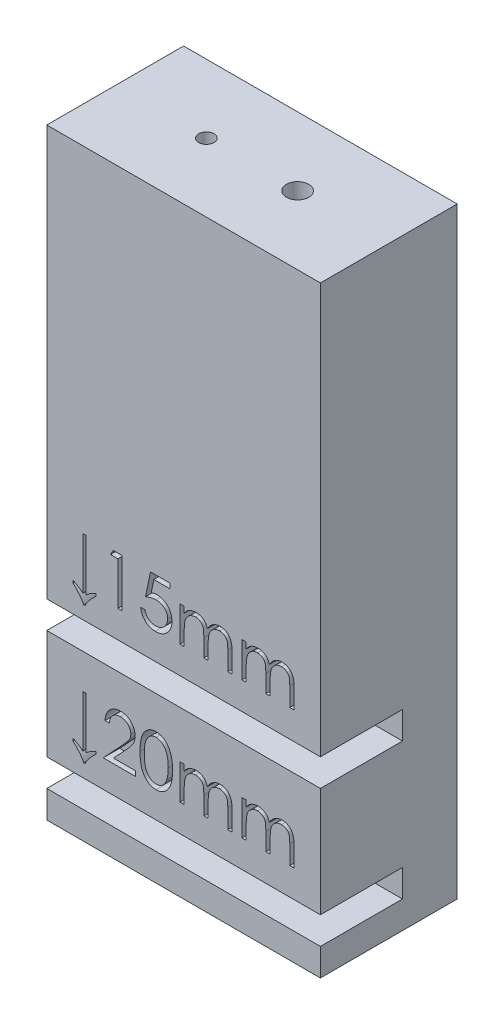
SolidWorks part; units mm, degrees
ref_plane "Front" through (0, 0, 0) normal (0, 0, 1) x (1, 0, 0)
ref_plane "Top" through (0, 0, 0) normal (0, 1, 0) x (1, 0, 0)
ref_plane "Right" through (0, 0, 0) normal (1, 0, 0) x (0, 0, -1)
sketch "Sketch1" plane through (0, 0, 0) normal (0, 1, 0) x (1, 0, 0)
  line L1 (5, 2.5) -> (-5, 2.5)
  line L2 (5, 2.5) -> (5, -2.5)
  line L3 (5, -2.5) -> (-5, -2.5)
  line L4 (-5, 2.5) -> (-5, -2.5)
  line L5 (5, 2.5) -> (-5, -2.5) construction
  line L6 (5, -2.5) -> (-5, 2.5) construction
  point P0 (0, 0)
  dimension "D1" = 10
  dimension "D2" = 5
extrude "Boss-Extrude1" add sketch "Sketch1" along normal blind 22
sketch "Sketch2" plane through (0, 0, 0) normal (0, 1, 0) x (1, 0, 0)
  line L0 (-5, 0) -> (-1.6667, 0) construction
  line L2 (-5, 2.5) -> (-5, -2.5) construction
  line L3 (-1.6667, 0) -> (1.6667, 0) construction
  line L4 (1.6667, 0) -> (5, 0) construction
  line L5 (5, -2.5) -> (5, 2.5) construction
  circle A0 centre (1.6667, 0) radius 0.41
  circle A1 centre (-1.6667, 0) radius 0.28
  dimension "D1" = 0.82
  dimension "D2" = 0.56
extrude "Cut-Extrude2" cut sketch "Sketch2" against normal through all and the other way through all
sketch "Sketch3" plane through (0, 0, 2.5) normal (0, 0, 1) x (1, 0, 0)
  line L4 (-5, 22) -> (-5, 0) construction
  line L5 (5, 7) -> (-5, 7)
  line L6 (0, 22) -> (0, 2) construction
  line L7 (-5, 22) -> (5, 22) construction
  line L8 (-5, 2) -> (5, 2)
  line L9 (-5, 2) -> (-5, 1)
  line L10 (-5, 1) -> (5, 1)
  line L11 (5, 2) -> (5, 1)
  line L12 (-5, 2) -> (5, 1) construction
  line L13 (-5, 1) -> (5, 2) construction
  line L14 (5, 7) -> (5, 6)
  line L15 (-5, 22) -> (-5, 0) construction
  line L16 (5, 6) -> (-5, 6)
  line L17 (-5, 7) -> (-5, 6)
  line L18 (5, 7) -> (-5, 6) construction
  line L19 (5, 6) -> (-5, 7) construction
  line L20 (0, 1) -> (0, 0) construction
  point P0 (0, 6.5)
  point P10 (0, 2)
  point P13 (0, 1.5)
  dimension "D1" = 1
  dimension "D2" = 15
  dimension "D4" = 20
  dimension "D5" = 1
extrude "Cut-Extrude3" cut sketch "Sketch3" against normal offset from surface (3 mm away) 2 up to face at (0, 11, -2.5)
sketch "Sketch4" plane through (0, 0, 2.5) normal (0, 0, 1) x (1, 0, 0)
  line L0 (-4.5, 3) -> (4.5, 3) construction
  line L1 (5, 7) -> (-5, 7) construction
  line L2 (-5, 2) -> (5, 2) construction
  line L3 (-4.5, 8) -> (4.5, 8) construction
  text T0 "↓20mm" font "Century Gothic" height 1.75
  text T1 "↓15mm" font "Century Gothic" height 1.75
  point P1 (0, 3)
  point P9 (0, 8)
  point P12 (3.2876, 11)
  point P13 (0, 0)
  point P14 (0, 0)
  point P15 (-2.2227, 0.4013)
  point P16 (0, 0)
  dimension "D1" = 9
  dimension "D2" = 1
  dimension "D3" = 9
  dimension "D4" = 1
extrude "Cut-Extrude4" cut sketch "Sketch4" against normal blind 0.6
